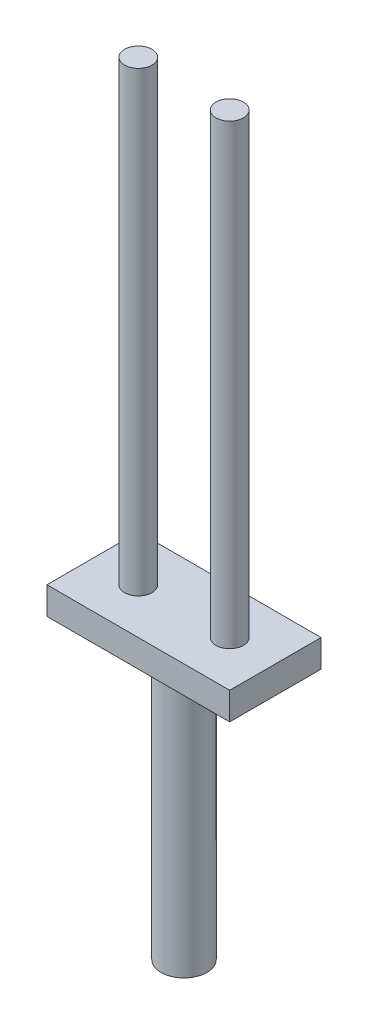
SolidWorks part; units mm, degrees
ref_plane "Front Plane" through (0, 0, 0) normal (0, 0, 1) x (1, 0, 0)
ref_plane "Top Plane" through (0, 0, 0) normal (0, 1, 0) x (1, 0, 0)
ref_plane "Right Plane" through (0, 0, 0) normal (1, 0, 0) x (0, 0, -1)
sketch "Sketch1" plane through (0, 0, 0) normal (0, 1, 0) x (1, 0, 0)
  line L0 (0, 5) -> (0, -5) construction
  line L1 (-10, 5) -> (10, 5)
  line L2 (-10, 5) -> (-10, -5)
  line L3 (-10, -5) -> (10, -5)
  line L4 (10, 5) -> (10, -5)
  line L5 (-10, 5) -> (10, -5) construction
  line L6 (-10, -5) -> (10, 5) construction
  line L7 (10, 0) -> (-10, 0) construction
  point P0 (0, 0)
  dimension "D1" = 10
  dimension "D2" = 20
extrude "Boss-Extrude1" add sketch "Sketch1" along normal blind 3
sketch "Sketch2" plane through (0, 3, 0) normal (0, 1, 0) x (1, 0, 0)
  line L0 (-10, 0) -> (10, 0) construction
  line L1 (-10, 5) -> (-10, -5) construction
  line L2 (10, -5) -> (10, 5) construction
  line L3 (0, 5) -> (0, -5) construction
  line L4 (10, 5) -> (-10, 5) construction
  line L5 (-10, -5) -> (10, -5) construction
  circle A0 centre (-5, 0) radius 1.5
  circle A1 centre (5, 0) radius 1.5
  dimension "D1" = 3
  dimension "D2" = 5
extrude "Boss-Extrude2" add sketch "Sketch2" along normal blind 50
sketch "Sketch3" plane through (0, 0, 0) normal (0, -1, 0) x (1, 0, 0)
  line L0 (0, 5) -> (0, -5) construction
  line L1 (-10, 5) -> (10, 5) construction
  line L2 (10, -5) -> (-10, -5) construction
  line L3 (-10, 0) -> (10, 0) construction
  line L4 (-10, -5) -> (-10, 5) construction
  line L5 (10, 5) -> (10, -5) construction
  circle A0 centre (0, 0) radius 2.5
  dimension "D1" = 5
extrude "Boss-Extrude3" add sketch "Sketch3" along normal blind 30
